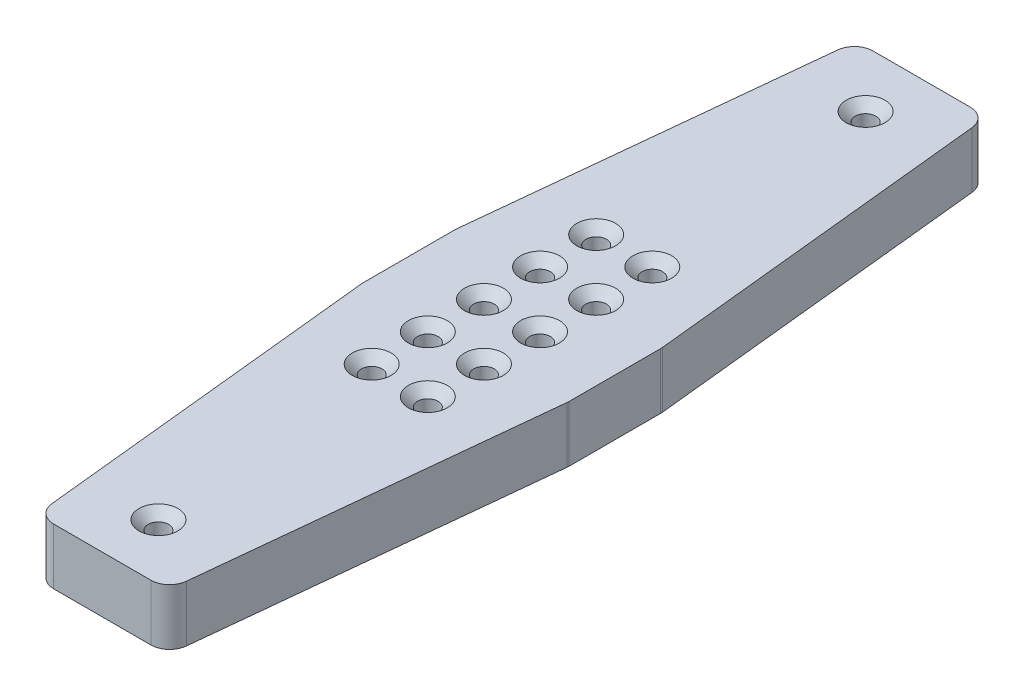
SolidWorks part; units mm, degrees
ref_plane "Plan de face" through (0, 0, 0) normal (0, 0, 1) x (1, 0, 0)
ref_plane "Plan de dessus" through (0, 0, 0) normal (0, 1, 0) x (1, 0, 0)
ref_plane "Plan de droite" through (0, 0, 0) normal (1, 0, 0) x (0, 0, -1)
sketch "Esquisse1" plane through (0, 0, 0) normal (0, 1, 0) x (1, 0, 0)
  line L0 (-17.5, 109.5) -> (-27.5, 12.5)
  line L2 (-27.5, -12.5) -> (-27.5, 12.5)
  line L4 (27.5, -12.5) -> (27.5, 12.5)
  line L5 (-27.5, -12.5) -> (27.5, 12.5) construction
  line L6 (-27.5, 12.5) -> (27.5, -12.5) construction
  line L7 (17.5, -109.5) -> (-17.5, -109.5)
  line L9 (17.5, 109.5) -> (-17.5, 109.5)
  line L11 (17.5, -109.5) -> (-17.5, 109.5) construction
  line L12 (17.5, 109.5) -> (-17.5, -109.5) construction
  line L13 (17.5, 109.5) -> (27.5, 12.5)
  line L14 (-27.5, -12.5) -> (-17.5, -109.5)
  line L15 (27.5, -12.5) -> (17.5, -109.5)
  point P0 (0, 0)
  point P6 (0, 0)
  point P12 (0, -109.5)
  point P13 (0, 109.5)
  dimension "D1" = 25
  dimension "D2" = 55
  dimension "D3" = 35
  dimension "D4" = 97
extrude "Boss.-Extru.1" add sketch "Esquisse1" along normal blind 15
hole_wizard "Fraisage pour vis à tête fraisée M51" positions "Esquisse2" profile "Esquisse3" countersink size "M5" standard "Ansi Metric" end condition through all
sketch "Esquisse2" plane through (0, 15, 0) normal (0, 1, 0) x (1, 0, 0)
  line L0 (0, 109.5) -> (0, -109.5) construction
  line L1 (17.5, 109.5) -> (-17.5, 109.5) construction
  line L2 (-17.5, -109.5) -> (17.5, -109.5) construction
  line L5 (-7.5, -30) -> (7.5, 30) construction
  line L7 (-7.5, 30) -> (7.5, -30) construction
  point P0 (-7.5, 30)
  point P2 (7.5, 30)
  point P4 (7.5, 15)
  point P6 (-7.5, 15)
  point P8 (-7.5, 0)
  point P10 (7.5, 0)
  point P12 (7.5, -15)
  point P14 (-7.5, -15)
  point P35 (-7.5, -30)
  point P37 (7.5, -30)
  point P56 (0, 0)
  point P58 (0, -94.5)
  point P60 (0, 94.5)
  dimension "D1" = 15
  dimension "D2" = 15
  dimension "D3" = 15
  dimension "D4" = 15
  dimension "D5" = 15
  dimension "D6" = 15
  dimension "D7" = 15
sketch "Esquisse3" plane through (-7.5, 15, -30) normal (1, 0, 0) x (0, 0, 1)
  line L0 (0, 0) -> (0, 15)
  line L1 (0, 15) -> (2.75, 15)
  line L2 (2.75, 15) -> (2.75, 2.45)
  line L3 (2.75, 2.45) -> (5.2, 0)
  line L5 (5.2, 0) -> (0, 0)
  line L6 (-2.75, 2.45) -> (-5.2, 0) construction
  line L11 (0, -6.35) -> (0, 107.95) construction
  dimension "Diamètre du perçage jusqu'au prochain" = 5.5
  dimension "Profondeur du perçage jusqu'au prochain" = 15
  dimension "Diamètre du fraisage entrant" = 10.4
  dimension "Angle du fraisage entrant" = 90
fillet "Congé2" radius 5 8 edges at (-27.5, 7.5, -12.5) (-27.5, 7.5, 12.5) (-17.5, 7.5, 109.5) (17.5, 7.5, 109.5) (27.5, 7.5, 12.5) (27.5, 7.5, -12.5) (-17.5, 7.5, -109.5) (17.5, 7.5, -109.5)
